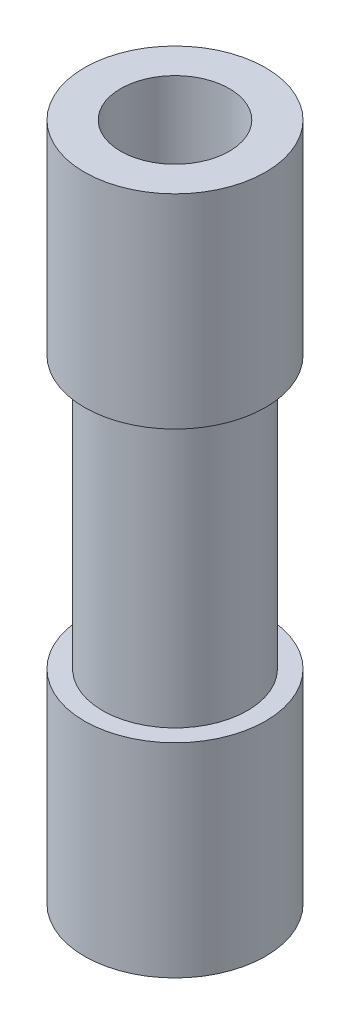
SolidWorks part; units mm, degrees
ref_plane "Front Plane" through (0, 0, 0) normal (0, 0, 1) x (1, 0, 0)
ref_plane "Top Plane" through (0, 0, 0) normal (0, 1, 0) x (1, 0, 0)
ref_plane "Right Plane" through (0, 0, 0) normal (1, 0, 0) x (0, 0, -1)
sketch "Sketch2" plane through (0, 0, 0) normal (0, 1, 0) x (1, 0, 0)
  circle A0 centre (0, 0) radius 1
extrude "Boss-Extrude1" add sketch "Sketch2" along normal blind 7.5
ref_plane "Plane1" through (0, 3.75, 0) normal (0, 1, 0) x (1, 0, 0)
sketch "Sketch4" plane through (0, 3.75, 0) normal (0, 1, 0) x (1, 0, 0)
  circle A0 centre (0, 0) radius 0.8
  dimension "D1" = 1.6
extrude "Cut-Extrude1" cut sketch "Sketch4" against normal blind 1.5 and the other way blind 1.5 flip side to cut
sketch "Sketch5" plane through (0, 7.5, 0) normal (0, 1, 0) x (1, 0, 0)
  circle A0 centre (0, 0) radius 0.6
  dimension "D1" = 1.2
extrude "Cut-Extrude2" cut sketch "Sketch5" against normal blind 7.5
